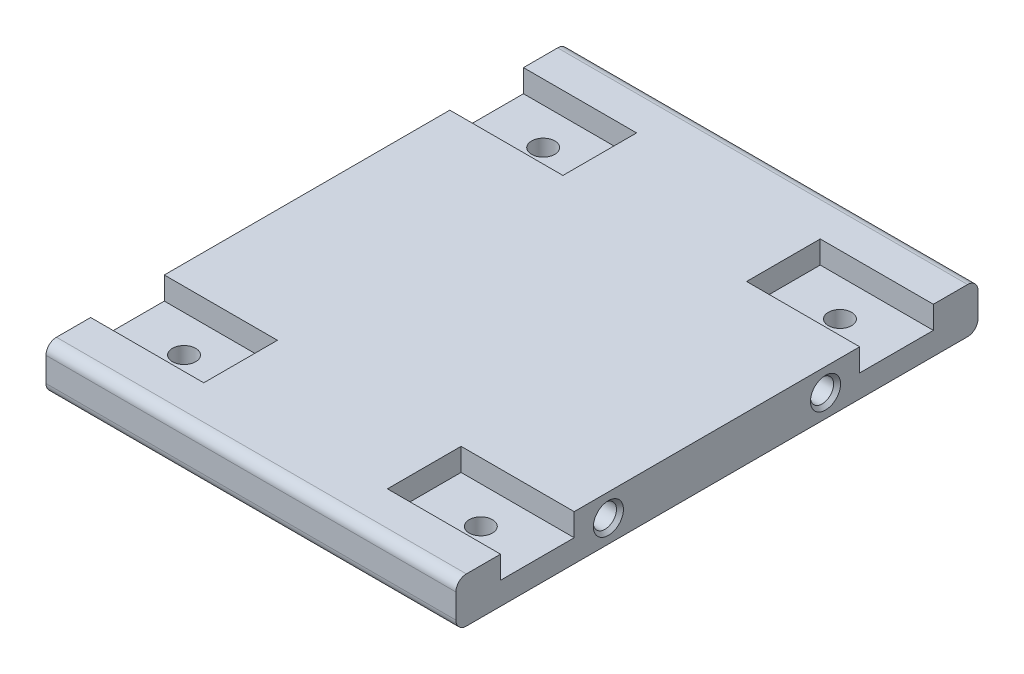
SolidWorks part; units mm, degrees
material "ABS"
ref_plane "Front Plane" through (0, 0, 0) normal (0, 0, 1) x (1, 0, 0)
ref_plane "Top Plane" through (0, 0, 0) normal (0, 1, 0) x (1, 0, 0)
ref_plane "Right Plane" through (0, 0, 0) normal (1, 0, 0) x (0, 0, -1)
sketch "Sketch1" plane through (0, 0, 0) normal (0, 1, 0) x (1, 0, 0)
  line L1 (-58.8828, -75) -> (58.8828, -75)
  line L2 (-58.8828, -75) -> (-58.8828, 75)
  line L3 (-58.8828, 75) -> (58.8828, 75)
  line L4 (58.8828, -75) -> (58.8828, 75)
  line L5 (-58.8828, -75) -> (58.8828, 75) construction
  line L6 (-58.8828, 75) -> (58.8828, -75) construction
  point P0 (0, 0)
  dimension "D1" = 117.7655
  dimension "D2" = 150
extrude "Boss-Extrude1" add sketch "Sketch1" along normal blind 13
fillet "Fillet1" radius 3 4 edges at (0, 0, -75) (0, 13, -75) (0, 0, 75) (0, 13, 75)
sketch "Sketch2" plane through (-58.8828, 0, 0) normal (-1, 0, 0) x (0, 0, 1)
  line L0 (0, 0) -> (0, 13) construction
  line L1 (-72, 0) -> (72, 0) construction
  line L2 (-72, 13) -> (72, 13) construction
  line L3 (-75, 6.5) -> (75, 6.5) construction
  line L4 (-75, 10) -> (-75, 3) construction
  line L5 (75, 10) -> (75, 3) construction
  line L6 (-62.1769, 13) -> (-62.1769, 6.5)
  line L7 (-62.1769, 6.5) -> (-41.0121, 6.5)
  line L8 (-41.0121, 6.5) -> (-41.0121, 13)
  line L9 (-41.0121, 13) -> (-62.1769, 13)
  line L10 (41.0121, 6.5) -> (41.0121, 13)
  line L11 (62.1769, 6.5) -> (41.0121, 6.5)
  line L12 (41.0121, 13) -> (62.1769, 13)
  line L13 (62.1769, 13) -> (62.1769, 6.5)
  circle A0 centre (-31.189, 6.5) radius 3.325
  circle A1 centre (31.189, 6.5) radius 3.325
  point P14 (-51.5945, 13)
  line M12 (72, 13) -> (-72, 13)
  dimension "D3" = 6.65
  dimension "D1" = 21.1649
  dimension "D2" = 51.5945
  dimension "D4" = 20.4055
extrude "Cut-Extrude1" cut sketch "Sketch2" against normal blind 32.5 contours L7 L8 L6 M12 | L13 L10 L11 M12
sketch "Sketch3" plane through (0, 6.5, 0) normal (0, 1, 0) x (1, 0, 0)
  line L0 (-42.6328, 62.1769) -> (-42.6328, 41.0121) construction
  line L1 (-26.3828, 62.1769) -> (-58.8828, 62.1769) construction
  line L2 (-26.3828, 41.0121) -> (-58.8828, 41.0121) construction
  line L3 (-58.8828, 51.5945) -> (-26.3828, 51.5945) construction
  line L4 (-58.8828, 62.1769) -> (-58.8828, 41.0121) construction
  line L6 (0, 0) -> (-58.8828, 0) construction
  line L7 (-58.8828, 41.0121) -> (-58.8828, -41.0121) construction
  line L8 (-26.3828, 41.0121) -> (-26.3828, 62.1769) construction
  circle A0 centre (-42.6328, 51.5945) radius 3.35
  circle A1 centre (-42.6328, -51.5945) radius 3.35
  dimension "D1" = 6.7
extrude "Cut-Extrude2" cut sketch "Sketch3" against normal up to surface (6.5 mm away) up to face at (0, 0, 0)
mirror "Mirror1" about plane through (0, 0, 0) normal (1, 0, 0) of "Cut-Extrude2", "Cut-Extrude1"
sketch "Sketch4" plane through (-58.8828, 0, 0) normal (-1, 0, 0) x (0, 0, 1)
  circle A0 centre (31.189, 6.5) radius 3.325 construction
  circle A1 centre (-31.189, 6.5) radius 3.325 construction
  circle A2 centre (31.189, 6.5) radius 3.325
  circle A3 centre (-31.189, 6.5) radius 3.325
extrude "Cut-Extrude3" cut sketch "Sketch4" against normal up to surface (117.7655 mm away) up to face at (58.8828, 8.125, 0)
chamfer "Chamfer1" distance 1 angle 45 4 edges at (58.8828, 6.5, 34.514) (58.8828, 6.5, -27.864) (-58.8828, 6.5, 34.514) (-58.8828, 6.5, -27.864)
sketch3d "3DSketch1"
  line L0 (-58.8828, 13, 72) -> (58.8828, 13, 72) construction
  line L1 (58.8828, 13, -72) -> (-58.8828, 13, -72) construction
  line L2 (-58.8828, 13, 72) -> (58.8828, 13, 72)
  line L3 (58.8828, 13, -72) -> (-58.8828, 13, -72)
  line L4 (0, 13, -72) -> (0, 13, 72) construction
  point P6 (0, 0, 0)
